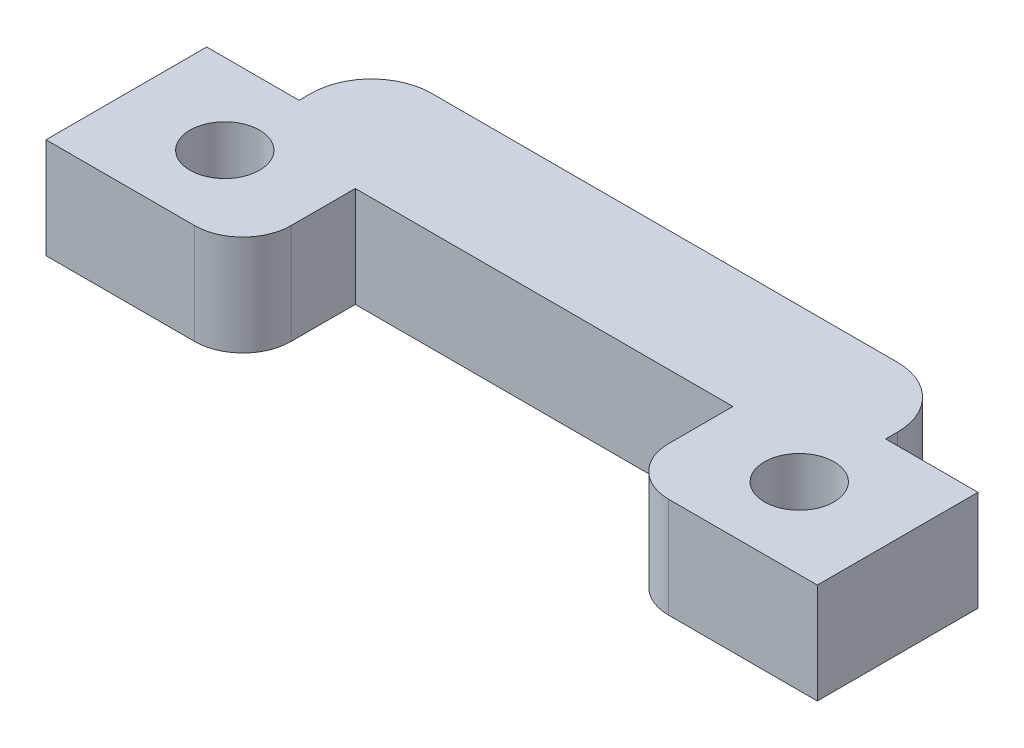
SolidWorks part; units mm, degrees
ref_plane "Front Plane" through (0, 0, 0) normal (0, 0, 1) x (1, 0, 0)
ref_plane "Top Plane" through (0, 0, 0) normal (0, 1, 0) x (1, 0, 0)
ref_plane "Right Plane" through (0, 0, 0) normal (1, 0, 0) x (0, 0, -1)
sketch "Sketch1" plane through (0, 0, 0) normal (0, 1, 0) x (1, 0, 0)
  line L0 (0, -0.1272) -> (4.699, -0.1272)
  line L1 (19.685, -0.1272) -> (24.384, -0.1272)
  line L2 (24.384, -0.1272) -> (24.384, 7.2388)
  line L3 (24.384, 7.2388) -> (0, 7.2388)
  line L4 (0, 7.2388) -> (0, -0.1272)
  line L5 (18.161, 1.3968) -> (18.161, 3.4288)
  line L6 (18.161, 3.4288) -> (6.223, 3.4288)
  line L7 (6.223, 3.4288) -> (6.223, 1.3968)
  arc A0 (4.699, -0.1272) -> (6.223, 1.3968) centre (4.699, 1.3968) ccw
  arc A1 (18.161, 1.3968) -> (19.685, -0.1272) centre (19.685, 1.3968) ccw
  dimension "D1" = 24.384
  dimension "D2" = 3.81
  dimension "D3" = 7.366
  dimension "D4" = 4.699
  dimension "D5" = 4.699
  dimension "D6" = 11.938
  dimension "D7" = 2.032
  dimension "D8" = 6.223
extrude "Boss-Extrude1" add sketch "Sketch1" along normal blind 3.175
hole_wizard "M2 Clearance Hole1" positions "Sketch2" profile "Sketch3" hole size "M2" standard "ANSI Metric" end condition through all
sketch "Sketch2" plane through (0, 0, 0) normal (0, -1, 0) x (-1, 0, 0)
  point P0 (-3.1115, 2.4128)
  point P2 (-21.2725, 2.4128)
sketch "Sketch3" plane through (3.1115, 0, -2.4128) normal (1, 0, 0) x (0, 0, -1)
  line L0 (0, 0) -> (0, 3.175)
  line L1 (0, 3.175) -> (1.1, 3.175)
  line L2 (1.1, 3.175) -> (1.1, 0)
  line L5 (1.1, 0) -> (0, 0)
  line L11 (0, -6.35) -> (0, 107.95) construction
  dimension "Thru Hole Dia." = 2.2
  dimension "Thru Hole Depth" = 3.175
sketch "Sketch4" plane through (0, 0, 0) normal (0, -1, 0) x (1, 0, 0)
  line L1 (24.384, -7.2388) -> (21.463, -7.2388)
  line L2 (24.384, -7.2388) -> (24.384, -4.9528)
  line L3 (24.384, -4.9528) -> (21.463, -4.9528)
  line L4 (21.463, -7.2388) -> (21.463, -4.9528)
  line L5 (0, -7.2388) -> (2.921, -7.2388)
  line L6 (0, -7.2388) -> (0, -4.9528)
  line L7 (0, -4.9528) -> (2.921, -4.9528)
  line L8 (2.921, -7.2388) -> (2.921, -4.9528)
extrude "Cut-Extrude1" cut sketch "Sketch4" against normal through all
fillet "Fillet1" radius 1.905 2 edges at (2.921, 1.5875, -7.2388) (21.463, 1.5875, -7.2388)
